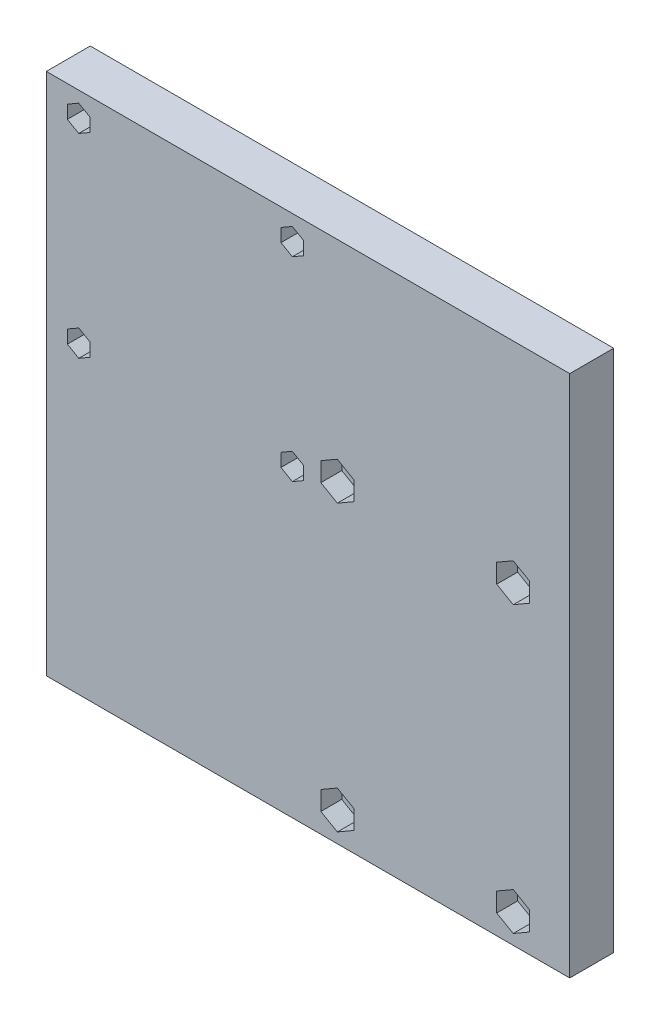
SolidWorks part; units mm, degrees
ref_plane "Front Plane" through (0, 0, 0) normal (0, 0, 1) x (1, 0, 0)
ref_plane "Top Plane" through (0, 0, 0) normal (0, 1, 0) x (1, 0, 0)
ref_plane "Right Plane" through (0, 0, 0) normal (1, 0, 0) x (0, 0, -1)
sketch "Sketch2" plane through (0, 0, 0) normal (0, 0, 1) x (1, 0, 0)
  line L0 (84.7517, 5.33) -> (84.7517, -16.67) construction
  line L1 (91.7517, -74.67) -> (-33.2483, -74.67)
  line L2 (91.7517, -74.67) -> (91.7517, 50.33)
  line L3 (91.7517, 50.33) -> (-33.2483, 50.33)
  line L4 (-33.2483, -74.67) -> (-33.2483, 50.33)
  line L5 (84.7517, 5.33) -> (29.7517, 5.33) construction
  line L6 (25.5, 44.5) -> (-25.5, 44.5) construction
  line L7 (-25.5, -2) -> (-25.5, 44.5) construction
  circle A0 centre (-25.5, -2) radius 1.5 construction
  circle A1 centre (25.5, -2) radius 1.5 construction
  circle A2 centre (78.2517, 0.33) radius 2.5 construction
  circle A3 centre (36.2517, 0.33) radius 2.5 construction
  circle A4 centre (36.2517, -67.67) radius 2.5 construction
  circle A5 centre (78.2517, -67.67) radius 2.5 construction
  circle A6 centre (-25.5, -2) radius 1.5
  circle A7 centre (25.5, -2) radius 1.5
  circle A8 centre (78.2517, 0.33) radius 2.5
  circle A9 centre (36.2517, 0.33) radius 2.5
  circle A10 centre (36.2517, -67.67) radius 2.5
  circle A11 centre (78.2517, -67.67) radius 2.5
  circle A12 centre (25.5, 44.5) radius 1.5
  circle A13 centre (-25.5, 44.5) radius 1.5
  arc A14 (27, 44.5) -> (24, 44.5) centre (25.5, 44.5) ccw construction
  dimension "D1" = 125
  dimension "D2" = 125
  dimension "D3" = 7
  dimension "D4" = 45
extrude "Boss-Extrude1" add sketch "Sketch2" along normal blind 10.5
sketch "Sketch3" plane through (0, 0, 10.5) normal (0, 0, 1) x (1, 0, 0)
  line L1 (74.3167, -69.9419) -> (78.2517, -72.2137)
  line L2 (78.2517, -72.2137) -> (82.1867, -69.9419)
  line L3 (82.1867, -69.9419) -> (82.1867, -65.3981)
  line L4 (82.1867, -65.3981) -> (78.2517, -63.1263)
  line L5 (78.2517, -63.1263) -> (74.3167, -65.3981)
  line L6 (74.3167, -65.3981) -> (74.3167, -69.9419)
  line L7 (36.2517, -72.2137) -> (40.1867, -69.9419)
  line L8 (40.1867, -69.9419) -> (40.1867, -65.3981)
  line L9 (40.1867, -65.3981) -> (36.2517, -63.1263)
  line L10 (36.2517, -63.1263) -> (32.3167, -65.3981)
  line L11 (32.3167, -65.3981) -> (32.3167, -69.9419)
  line L12 (32.3167, -69.9419) -> (36.2517, -72.2137)
  line L13 (36.2517, -4.2137) -> (40.1867, -1.9419)
  line L14 (40.1867, -1.9419) -> (40.1867, 2.6019)
  line L15 (40.1867, 2.6019) -> (36.2517, 4.8737)
  line L16 (36.2517, 4.8737) -> (32.3167, 2.6019)
  line L17 (32.3167, 2.6019) -> (32.3167, -1.9419)
  line L18 (32.3167, -1.9419) -> (36.2517, -4.2137)
  line L19 (78.2517, -4.2137) -> (82.1867, -1.9419)
  line L20 (82.1867, -1.9419) -> (82.1867, 2.6019)
  line L21 (82.1867, 2.6019) -> (78.2517, 4.8737)
  line L22 (78.2517, 4.8737) -> (74.3167, 2.6019)
  line L23 (74.3167, 2.6019) -> (74.3167, -1.9419)
  line L24 (74.3167, -1.9419) -> (78.2517, -4.2137)
  line L25 (22.785, -3.5675) -> (25.5, -5.135)
  line L26 (25.5, -5.135) -> (28.215, -3.5675)
  line L27 (28.215, -3.5675) -> (28.215, -0.4325)
  line L28 (28.215, -0.4325) -> (25.5, 1.135)
  line L29 (25.5, 1.135) -> (22.785, -0.4325)
  line L30 (22.785, -0.4325) -> (22.785, -3.5675)
  line L31 (-28.215, -3.5675) -> (-25.5, -5.135)
  line L32 (-25.5, -5.135) -> (-22.785, -3.5675)
  line L33 (-22.785, -3.5675) -> (-22.785, -0.4325)
  line L34 (-22.785, -0.4325) -> (-25.5, 1.135)
  line L35 (-25.5, 1.135) -> (-28.215, -0.4325)
  line L36 (-28.215, -0.4325) -> (-28.215, -3.5675)
  line L37 (22.785, 42.9325) -> (25.5, 41.365)
  line L38 (25.5, 41.365) -> (28.215, 42.9325)
  line L39 (28.215, 42.9325) -> (28.215, 46.0675)
  line L40 (28.215, 46.0675) -> (25.5, 47.635)
  line L41 (25.5, 47.635) -> (22.785, 46.0675)
  line L42 (22.785, 46.0675) -> (22.785, 42.9325)
  line L43 (-28.215, 42.9325) -> (-25.5, 41.365)
  line L44 (-25.5, 41.365) -> (-22.785, 42.9325)
  line L45 (-22.785, 42.9325) -> (-22.785, 46.0675)
  line L46 (-22.785, 46.0675) -> (-25.5, 47.635)
  line L47 (-25.5, 47.635) -> (-28.215, 46.0675)
  line L48 (-28.215, 46.0675) -> (-28.215, 42.9325)
  circle A0 centre (78.2517, -67.67) radius 3.935 construction
  circle A1 centre (36.2517, -67.67) radius 3.935 construction
  circle A2 centre (36.2517, 0.33) radius 3.935 construction
  circle A3 centre (78.2517, 0.33) radius 3.935 construction
  circle A4 centre (25.5, -2) radius 2.715 construction
  circle A5 centre (-25.5, -2) radius 2.715 construction
  circle A6 centre (25.5, 44.5) radius 2.715 construction
  circle A7 centre (-25.5, 44.5) radius 2.715 construction
  point P64 (74.3167, -67.67)
  dimension "D1" = 7.87
  dimension "D2" = 5.43
extrude "Cut-Extrude1" cut sketch "Sketch3" against normal blind 5
